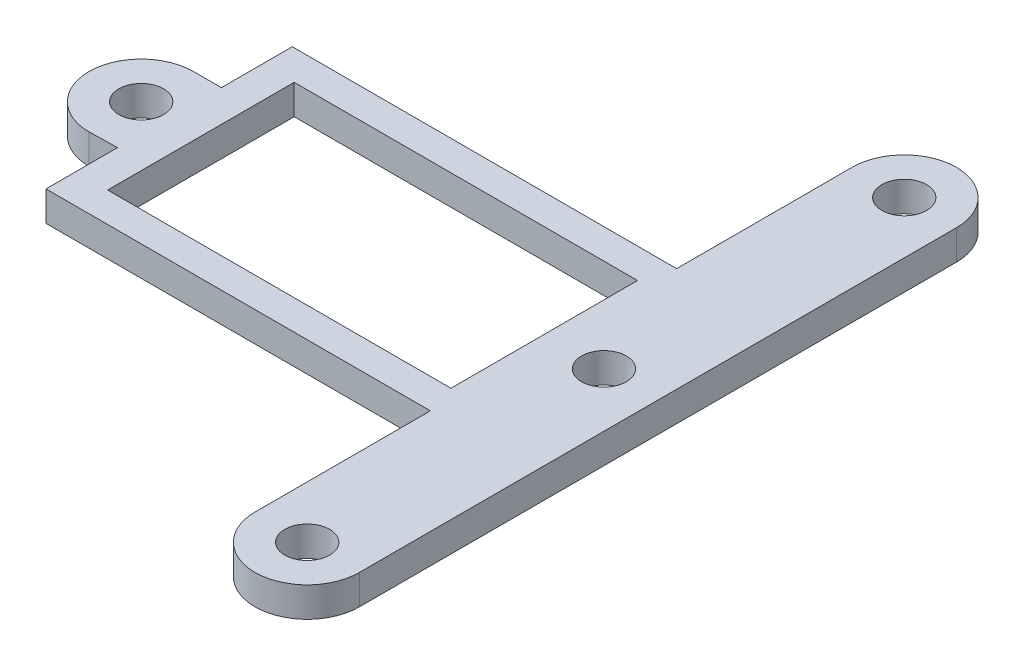
SolidWorks part; units mm, degrees
ref_plane "Front Plane" through (0, 0, 0) normal (0, 0, 1) x (1, 0, 0)
ref_plane "Top Plane" through (0, 0, 0) normal (0, 1, 0) x (1, 0, 0)
ref_plane "Right Plane" through (0, 0, 0) normal (1, 0, 0) x (0, 0, -1)
sketch "Sketch1" plane through (0, 0, 0) normal (0, 1, 0) x (1, 0, 0)
  line L0 (-10.99, 3.5) -> (-9.12, 3.5)
  line L1 (-10.99, -3.5) -> (-9.12, -3.4578)
  line L5 (-9.12, 8.25) -> (16.63, 8.25)
  line L6 (16.63, 8.25) -> (16.63, -8.25)
  line L7 (16.63, -8.25) -> (-9.12, -8.25)
  line L8 (-9.12, -8.25) -> (-9.12, 0)
  line L9 (-9.12, 0) -> (-9.12, 8.25)
  line L14 (16.63, 20) -> (16.63, 8.25)
  line L15 (23.63, 20) -> (23.63, 0)
  line L16 (49.9853, 0) -> (-49.079, 0) construction
  line L18 (16.63, -20) -> (16.63, -8.25)
  line L19 (23.63, -20) -> (23.63, 0)
  circle A0 centre (20.01, 0) radius 1.5
  circle A1 centre (-10.99, 0) radius 1.5
  circle A2 centre (-10.99, 0) radius 3.5
  circle A5 centre (20.13, 20) radius 1.5
  circle A6 centre (20.13, 20) radius 3.5
  circle A7 centre (20.13, -20) radius 3.5
  circle A8 centre (20.13, -20) radius 1.5
  dimension "D3" = 31
  dimension "D4" = 2
  dimension "D10" = 3
  dimension "D2" = 3.62
  dimension "D12" = 20
  dimension "D11" = 2
extrude "Boss-Extrude1" add sketch "Sketch1" along normal blind 2
sketch "Sketch2" plane through (0, 2, 0) normal (0, 1, 0) x (1, 0, 0)
  line L1 (16.01, 6.25) -> (-6.99, 6.25)
  line L2 (16.01, 6.25) -> (16.01, -6.25)
  line L3 (16.01, -6.25) -> (-6.99, -6.25)
  line L4 (-6.99, 6.25) -> (-6.99, -6.25)
  line L6 (23.63, -20) -> (23.63, 20) construction
  line L9 (-9.12, 8.25) -> (16.63, 8.25) construction
  line L10 (16.63, -8.25) -> (-9.12, -8.25) construction
  dimension "D1" = 7.62
  dimension "D2" = 12.5
  dimension "D3" = 23
  dimension "D4" = 2
  dimension "D5" = 2
extrude "Cut-Extrude1" cut sketch "Sketch2" against normal through all
